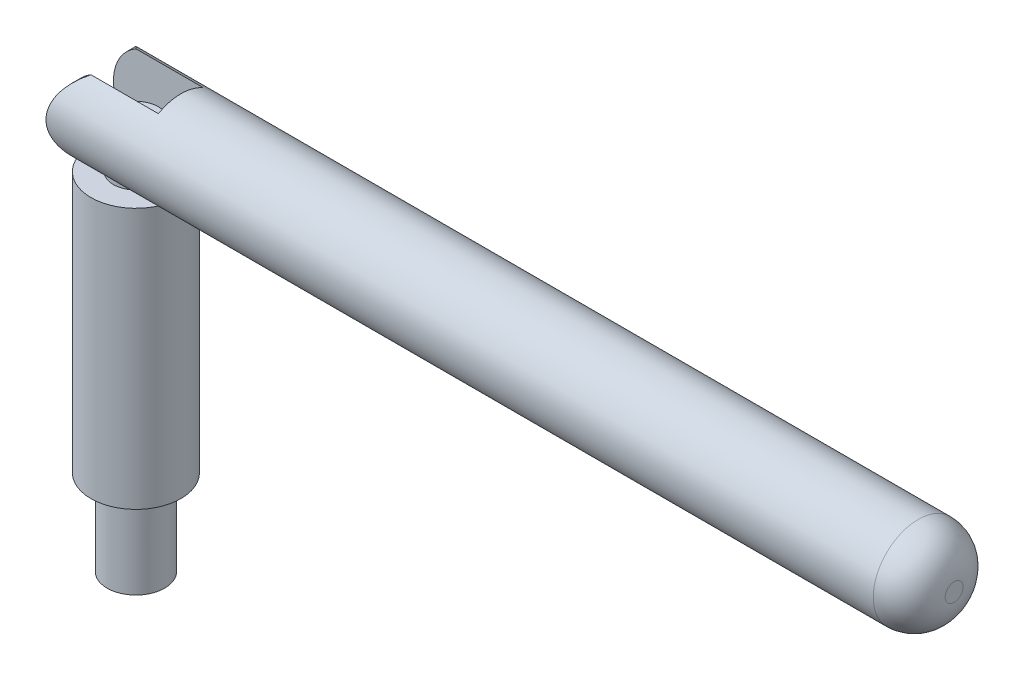
SolidWorks part; units mm, degrees
material "CA"
ref_plane "Front Plane" through (0, 0, 0) normal (0, 0, 1) x (1, 0, 0)
ref_plane "Top Plane" through (0, 0, 0) normal (0, 1, 0) x (1, 0, 0)
ref_plane "Right Plane" through (0, 0, 0) normal (1, 0, 0) x (0, 0, -1)
sketch "Sketch1" plane through (0, 0, 0) normal (0, 1, 0) x (1, 0, 0)
  circle A0 centre (0, 0) radius 5
  dimension "D1" = 10
extrude "Boss-Extrude1" add sketch "Sketch1" along normal blind 29
sketch "Sketch2" plane through (0, 29, 0) normal (0, 1, 0) x (1, 0, 0)
  circle A0 centre (0, 0) radius 2.5
  dimension "D1" = 5
extrude "Boss-Extrude2" add sketch "Sketch2" along normal blind 5
sketch "Sketch4" plane through (0, 0, 0) normal (0, -1, 0) x (1, 0, 0)
  circle A0 centre (0, 0) radius 3.2
  dimension "D1" = 6.4
extrude "Boss-Extrude3" add sketch "Sketch4" along normal blind 9.525
ref_plane "Plane1" through (5, 0, 0) normal (1, 0, 0) x (0, 0, -1)
sketch "Sketch5" plane through (5, 0, 0) normal (1, 0, 0) x (0, 0, -1)
  line L0 (2.5, 34) -> (-2.5, 34) construction
  circle A0 centre (0, 34) radius 5
  dimension "D1" = 10
extrude "Boss-Extrude4" add sketch "Sketch5" along normal blind 86 and the other way blind 10 separate body
fillet "Fillet1" radius 4 1 edges at (91, 34, -5)
sketch "Sketch8" plane through (0, 29, 0) normal (0, 1, 0) x (1, 0, 0)
  line L0 (0, 0) -> (5, 0) construction
  line L1 (5, 2.5) -> (5, -2.5)
  line L2 (5, -2.5) -> (-5, -2.5)
  line L3 (-5, -2.5) -> (-5, 2.5)
  line L4 (-5, 0) -> (0, 0) construction
  line L5 (5, 2.5) -> (-5, 2.5)
  dimension "D1" = 5
  dimension "D2" = 10
  dimension "D3" = 2.5
extrude "Cut-Extrude2" cut sketch "Sketch8" along normal through all
sketch "Sketch9" plane through (0, 0, 0) normal (0, 0, 1) x (1, 0, 0)
  line L0 (-5, 29) -> (-5, 34)
  line L1 (-5, 29) -> (0, 29)
  line L2 (-5, 34) -> (0, 34) construction
  line L3 (-5, 34) -> (-5, 39)
  line L4 (-5, 39) -> (0, 39)
  arc A0 (0, 39) -> (0, 29) centre (0, 34) ccw
  dimension "D1" = 5
extrude "Cut-Extrude3" cut sketch "Sketch9" against normal through all and the other way through all contours A0 L0 L1 | A0 L4 L3
